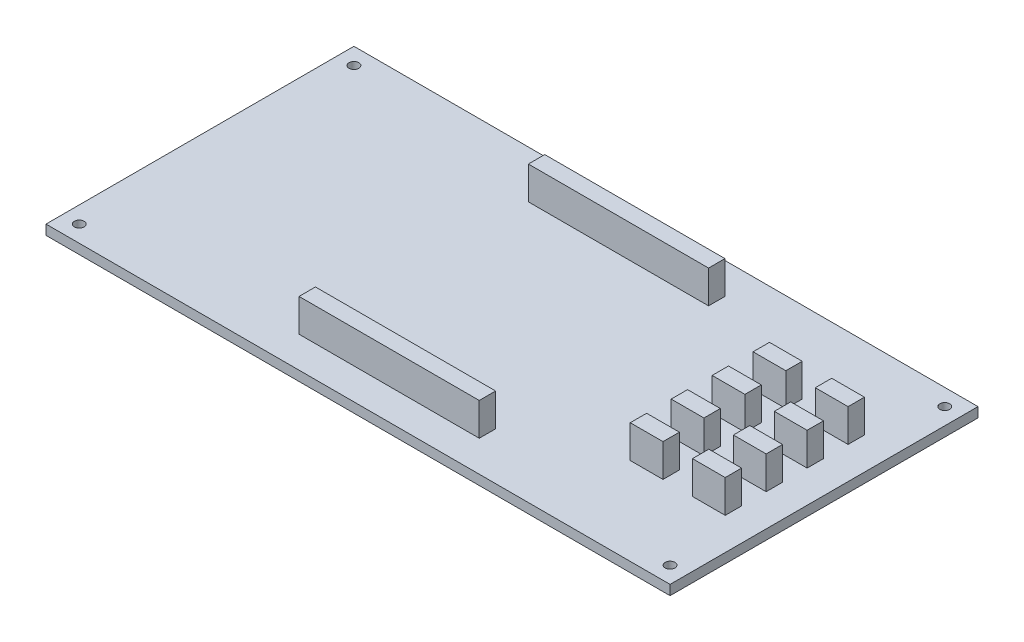
SolidWorks part; units mm, degrees
ref_plane "Face" through (0, 0, 0) normal (0, 0, 1) x (1, 0, 0)
ref_plane "Dessus" through (0, 0, 0) normal (0, 1, 0) x (1, 0, 0)
ref_plane "Droite" through (0, 0, 0) normal (1, 0, 0) x (0, 0, -1)
sketch "Esquisse1" plane through (0, 0, 0) normal (0, 1, 0) x (1, 0, 0)
  line L0 (95.25, 94) -> (95.25, 0) construction
  line L1 (0, 0) -> (190.5, 0)
  line L2 (0, 0) -> (0, 94)
  line L3 (0, 94) -> (190.5, 94)
  line L4 (190.5, 0) -> (190.5, 94)
  line L5 (0, 47) -> (190.5, 47) construction
  circle A0 centre (5.08, 88.92) radius 1.5
  circle A1 centre (185.42, 88.92) radius 1.5
  circle A2 centre (185.42, 5.08) radius 1.5
  circle A3 centre (5.08, 5.08) radius 1.5
  dimension "D3" = 3
  dimension "D1" = 94
  dimension "D2" = 190.5
  dimension "D4" = 5.08
  dimension "D5" = 5.08
extrude "Extrusion1" add sketch "Esquisse1" along normal blind 3
sketch "Esquisse2" plane through (0, 3, 0) normal (0, 1, 0) x (1, 0, 0)
  line L0 (67.75, 84.5) -> (67.75, 9.5) construction
  line L1 (67.75, 84.5) -> (122.75, 84.5)
  line L2 (67.75, 84.5) -> (67.75, 79.5)
  line L3 (67.75, 79.5) -> (122.75, 79.5)
  line L4 (122.75, 84.5) -> (122.75, 79.5)
  line L5 (67.75, 14.5) -> (122.75, 14.5)
  line L6 (67.75, 14.5) -> (67.75, 9.5)
  line L7 (67.75, 9.5) -> (122.75, 9.5)
  line L8 (122.75, 14.5) -> (122.75, 9.5)
  line L10 (122.75, 84.5) -> (122.75, 9.5) construction
  line L12 (95.25, 94) -> (95.25, 0) construction
  line L13 (190.5, 94) -> (0, 94) construction
  line L14 (0, 0) -> (190.5, 0) construction
  line L15 (0, 47) -> (190.5, 47) construction
  line L16 (0, 94) -> (0, 0) construction
  line L17 (190.5, 0) -> (190.5, 94) construction
  point P20 (67.75, 47)
  point P21 (95.25, 79.5)
  dimension "D1" = 65
  dimension "D2" = 5
  dimension "D4" = 55
extrude "Extrusion2" add sketch "Esquisse2" along normal blind 10
sketch "Esquisse4" plane through (0, 3, 0) normal (0, 1, 0) x (1, 0, 0)
  line L0 (170.6763, 69.1585) -> (180.6763, 69.1585)
  line L1 (151.6857, 69.1585) -> (161.6857, 69.1585)
  line L2 (151.6857, 69.1585) -> (151.6857, 64.1585)
  line L3 (151.6857, 64.1585) -> (161.6857, 64.1585)
  line L4 (161.6857, 69.1585) -> (161.6857, 64.1585)
  line L5 (151.6857, 44.1585) -> (161.6857, 44.1585)
  line L6 (151.6857, 44.1585) -> (151.6857, 39.1585)
  line L7 (151.6857, 39.1585) -> (161.6857, 39.1585)
  line L8 (161.6857, 44.1585) -> (161.6857, 39.1585)
  line L9 (151.6857, 31.6585) -> (161.6857, 31.6585)
  line L10 (151.6857, 31.6585) -> (151.6857, 26.6585)
  line L11 (151.6857, 26.6585) -> (161.6857, 26.6585)
  line L12 (161.6857, 31.6585) -> (161.6857, 26.6585)
  line L13 (151.6857, 56.6585) -> (161.6857, 56.6585)
  line L14 (151.6857, 56.6585) -> (151.6857, 51.6585)
  line L15 (151.6857, 51.6585) -> (161.6857, 51.6585)
  line L16 (161.6857, 56.6585) -> (161.6857, 51.6585)
  line L17 (170.6763, 69.1585) -> (170.6763, 64.1585)
  line L18 (170.6763, 64.1585) -> (180.6763, 64.1585)
  line L19 (180.6763, 69.1585) -> (180.6763, 64.1585)
  line L20 (170.6763, 44.1585) -> (180.6763, 44.1585)
  line L21 (170.6763, 44.1585) -> (170.6763, 39.1585)
  line L22 (170.6763, 39.1585) -> (180.6763, 39.1585)
  line L23 (180.6763, 44.1585) -> (180.6763, 39.1585)
  line L24 (170.6763, 31.6585) -> (180.6763, 31.6585)
  line L25 (170.6763, 31.6585) -> (170.6763, 26.6585)
  line L26 (170.6763, 26.6585) -> (180.6763, 26.6585)
  line L27 (180.6763, 31.6585) -> (180.6763, 26.6585)
  line L28 (170.6763, 56.6585) -> (180.6763, 56.6585)
  line L29 (170.6763, 56.6585) -> (170.6763, 51.6585)
  line L30 (170.6763, 51.6585) -> (180.6763, 51.6585)
  line L31 (180.6763, 56.6585) -> (180.6763, 51.6585)
  dimension "D1" = 10
  dimension "D2" = 5
  dimension "D3" = 7.5
  dimension "D4" = 7.5
  dimension "D5" = 7.5
  dimension "D6" = 10
  dimension "D7" = 5
  dimension "D8" = 7.5
  dimension "D9" = 7.5
  dimension "D10" = 7.5
extrude "Extrusion4" add sketch "Esquisse4" along normal blind 10
